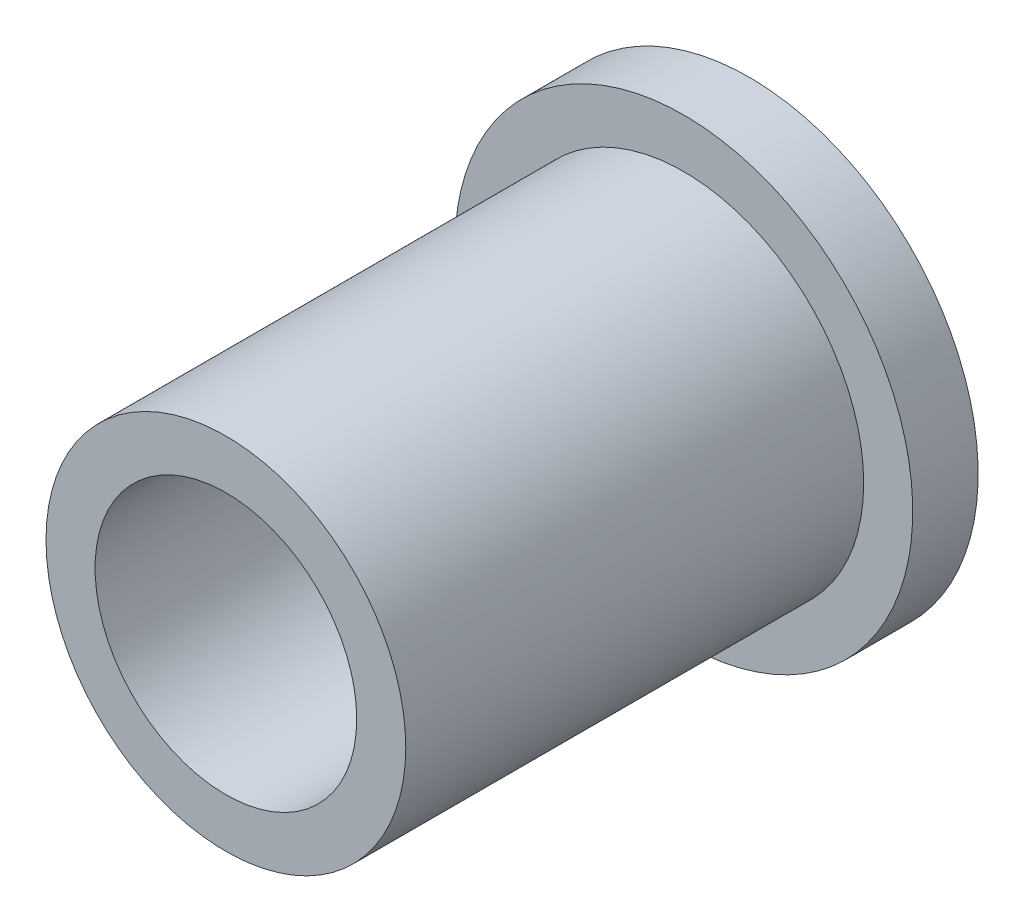
SolidWorks part; units mm, degrees
ref_plane "Plan de face" through (0, 0, 0) normal (0, 0, 1) x (1, 0, 0)
ref_plane "Plan de dessus" through (0, 0, 0) normal (0, 1, 0) x (1, 0, 0)
ref_plane "Plan de droite" through (0, 0, 0) normal (1, 0, 0) x (0, 0, -1)
sketch "Esquisse1" plane through (0, 0, 0) normal (0, 0, 1) x (1, 0, 0)
  circle A0 centre (0, 0) radius 2.75
  circle A1 centre (0, 0) radius 2
  dimension "D1" = 5.5
  dimension "D2" = 4
extrude "Boss.-Extru.1" add sketch "Esquisse1" along normal blind 8
cosmetic thread "Représentation de filetage2" parameters "D1"=7, "D2"=5
sketch "Esquisse2" plane through (0, 0, 0) normal (0, 0, -1) x (-1, 0, 0)
  circle A0 centre (0, 0) radius 2.75
  circle A1 centre (0, 0) radius 3.5
extrude "Boss.-Extru.2" add sketch "Esquisse2" against normal blind 1
